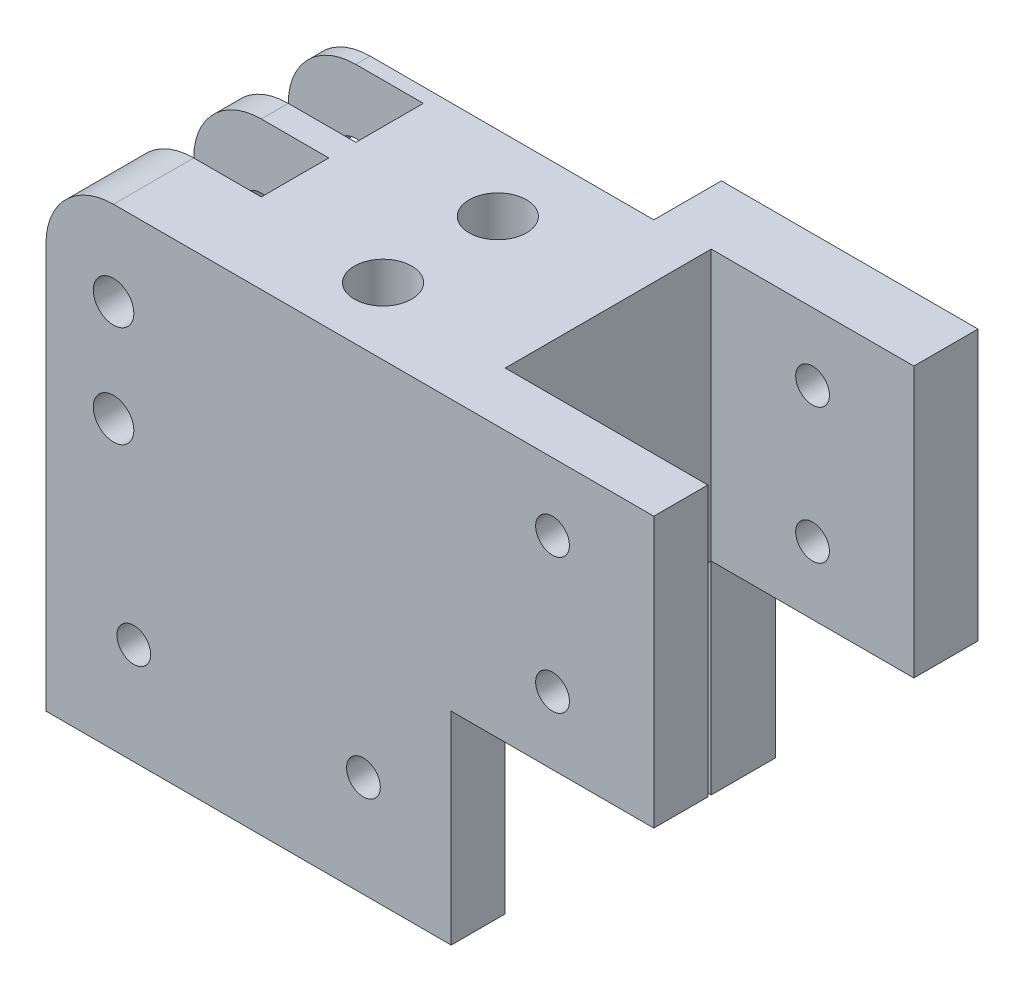
SolidWorks part; units mm, degrees
ref_plane "Front Plane" through (0, 0, 0) normal (0, 0, 1) x (1, 0, 0)
ref_plane "Top Plane" through (0, 0, 0) normal (0, 1, 0) x (1, 0, 0)
ref_plane "Right Plane" through (0, 0, 0) normal (1, 0, 0) x (0, 0, -1)
sketch "Esboço1" plane through (0, 0, 0) normal (0, 0, 1) x (1, 0, 0)
  line L0 (440, 72.2122) -> (440, 102.2122) construction
  line L1 (440, 72.2122) -> (380, 72.2122)
  line L2 (470, 102.2122) -> (470, 142.2122)
  line L3 (470, 142.2122) -> (390, 142.2122)
  line L4 (380, 72.2122) -> (380, 132.2122)
  line L5 (440, 102.2122) -> (470, 102.2122) construction
  line L6 (440, 72.2122) -> (440, 102.2122)
  line L7 (440, 102.2122) -> (470, 102.2122)
  line L9 (440, 87.2122) -> (380, 87.2122) construction
  line L10 (455, 102.2122) -> (455, 142.2122) construction
  arc A0 (390, 142.2122) -> (380, 132.2122) centre (390, 132.2122) ccw
  dimension "D1" = 10
  dimension "D2" = 40
  dimension "D3" = 60
extrude "Ressalto-extrusão1" add sketch "Esboço1" along normal blind 8 contours L4 A0 L3 L2 L7 L6 L1
hole_wizard "Broca de rosquear para tarraxa de M6x1.01" positions "Esboço2" profile "Esboço3" hole size "M6x1.0" standard "Ansi Metric" end condition through all
sketch "Esboço2" plane through (0, 0, 8) normal (0, 0, 1) x (1, 0, 0)
  line L0 (440, 87.2122) -> (380, 87.2122) construction
  line L1 (455, 102.2122) -> (455, 142.2122) construction
  line L2 (380, 72.2122) -> (380, 132.2122) construction
  line L3 (440, 72.2122) -> (440, 102.2122) construction
  line L4 (470, 142.2122) -> (390, 142.2122) construction
  point P0 (393, 87.2122)
  point P4 (427, 87.2122)
  point P6 (455, 112.2122)
  point P10 (455, 132.2122)
  dimension "D1" = 13
  dimension "D2" = 13
  dimension "D3" = 10
  dimension "D4" = 10
sketch "Esboço3" plane through (393, 87.2122, 8) normal (1, 0, 0) x (0, -1, 0)
  line L0 (0, 0) -> (0, 8)
  line L1 (0, 8) -> (2.5, 8)
  line L2 (2.5, 8) -> (2.5, 0)
  line L5 (2.5, 0) -> (0, 0)
  line L11 (0, -6.35) -> (0, 107.95) construction
  dimension "Thru Hole Dia." = 5
  dimension "Thru Hole Depth" = 8
sketch "Esboço4" plane through (0, 0, 0) normal (0, 0, -1) x (-1, 0, 0)
  line L0 (-470, 142.2122) -> (-390, 142.2122) construction
  line L1 (-390, 142.2122) -> (-440, 142.2122)
  line L2 (-380, 132.2122) -> (-380, 102.2122)
  line L3 (-380, 102.2122) -> (-440, 102.2122)
  line L4 (-440, 142.2122) -> (-440, 102.2122)
  line L5 (-380, 72.2122) -> (-380, 132.2122) construction
  arc A0 (-390, 142.2122) -> (-380, 132.2122) centre (-390, 132.2122) cw
  point P11 (-380, 142.2122)
  dimension "D1" = 10
extrude "Ressalto-extrusão2" add sketch "Esboço4" along normal blind 30
sketch "Esboço6" plane through (380, 0, 0) normal (-1, 0, 0) x (0, 0, 1)
  line L0 (-30, 142.2122) -> (0, 142.2122) construction
  line L1 (-27.8749, 102.2122) -> (-17.8749, 102.2122)
  line L2 (-27.8749, 102.2122) -> (-27.8749, 142.2122)
  line L3 (-27.8749, 142.2122) -> (-17.8749, 142.2122)
  line L4 (-17.8749, 102.2122) -> (-17.8749, 142.2122)
  line L5 (-13.8749, 117.2122) -> (-3.8749, 117.2122)
  line L6 (-13.8749, 117.2122) -> (-13.8749, 142.2122)
  line L7 (-13.8749, 142.2122) -> (-3.8749, 142.2122)
  line L8 (-3.8749, 117.2122) -> (-3.8749, 142.2122)
  dimension "D1" = 10
  dimension "D2" = 10
  dimension "D3" = 25
  dimension "D4" = 40
  dimension "D5" = 4
extrude "Corte-extrusão2" cut sketch "Esboço6" against normal blind 20
sketch "Esboço14" plane through (0, 0, -30) normal (0, 0, -1) x (-1, 0, 0)
  circle A2 centre (-390, 129.7122) radius 3
  circle A3 centre (-390, 129.7122) radius 3
  circle A5 centre (-390, 114.7122) radius 3
  circle A6 centre (-390, 114.7122) radius 3
  dimension "D1" = 0.5
  dimension "D2" = 0.5
extrude "Corte-extrusão6" cut sketch "Esboço14" against normal through all
sketch "Esboço15" plane through (0, 142.2122, 0) normal (0, 1, 0) x (1, 0, 0)
  circle A2 centre (420, 18.9024) radius 4.25
  circle A3 centre (420, 18.9024) radius 4.25
  circle A5 centre (420, 1.9024) radius 4.25
  circle A6 centre (420, 1.9024) radius 4.25
  dimension "D1" = 0
  dimension "D2" = 0
extrude "Corte-extrusão7" cut sketch "Esboço15" against normal up to surface (40 mm away) up to face at (400, 102.2122, -18.9374)
sketch "Esboço16" plane through (0, 0, -30) normal (0, 0, -1) x (-1, 0, 0)
  line L0 (-440, 142.2122) -> (-440, 102.2122) construction
  line L1 (-380, 102.2122) -> (-440, 102.2122)
  line L2 (-380, 102.2122) -> (-380, 110.2122)
  line L3 (-380, 110.2122) -> (-387.5457, 110.2122)
  line L4 (-440, 102.2122) -> (-440, 110.2122)
  line L5 (-394.815, 110.2122) -> (-432, 110.2122)
  line L7 (-432, 110.2122) -> (-432, 142.2122)
  line L8 (-432, 142.2122) -> (-440, 142.2122)
  line L9 (-440, 110.2122) -> (-440, 142.2122)
  arc A0 (-387.5457, 110.2122) -> (-394.815, 110.2122) centre (-391.1804, 113.8468) cw
  dimension "D1" = 8
  dimension "D2" = 8
extrude "Ressalto-extrusão3" add sketch "Esboço16" along normal blind 10
sketch "Esboço17" plane through (0, 102.2122, 0) normal (0, -1, 0) x (1, 0, 0)
  line L0 (440, -40) -> (440, 0) construction
  line L1 (380, -40) -> (440, -40)
  line L2 (380, -40) -> (380, -30.5)
  line L3 (380, -30.5) -> (440, -30.5)
  line L4 (440, -40) -> (440, -30.5)
  line L5 (440, -30) -> (0, -30) construction
  dimension "D1" = 0.5
extrude "Ressalto-extrusão4" add sketch "Esboço17" along normal through all
sketch "Esboço18" plane through (440, 0, 0) normal (1, 0, 0) x (0, 0, -1)
  line L0 (100, 102.2122) -> (-470, 102.2122) construction
  line L1 (40, 142.2122) -> (30.5, 142.2122)
  line L2 (40, 142.2122) -> (40, 102.2122)
  line L3 (40, 102.2122) -> (30.5, 102.2122)
  line L4 (30.5, 142.2122) -> (30.5, 102.2122)
  line L5 (30, 102.2122) -> (30, 542.2122) construction
  dimension "D1" = 0.5
extrude "Ressalto-extrusão5" add sketch "Esboço18" along normal through all
fillet "Filete1" radius 5 1 edges at (432, 110.2122, -35)
sketch "Esboço19" plane through (0, 0, -30.5) normal (0, 0, 1) x (1, 0, 0)
  circle A2 centre (455, 132.2122) radius 2.5
  circle A3 centre (455, 132.2122) radius 2.5
  circle A5 centre (455, 112.2122) radius 2.5
  circle A6 centre (455, 112.2122) radius 2.5
  dimension "D1" = 0
  dimension "D2" = 0
extrude "Corte-extrusão8" cut sketch "Esboço19" against normal blind 10
sketch "Esboço20" plane through (0, 0, -30.5) normal (0, 0, 1) x (1, 0, 0)
  circle A2 centre (427, 87.2122) radius 2.5
  circle A3 centre (427, 87.2122) radius 2.5
  circle A5 centre (393, 87.2122) radius 2.5
  circle A6 centre (393, 87.2122) radius 2.5
  dimension "D1" = 0
  dimension "D2" = 0
extrude "Corte-extrusão9" cut sketch "Esboço20" against normal blind 10
